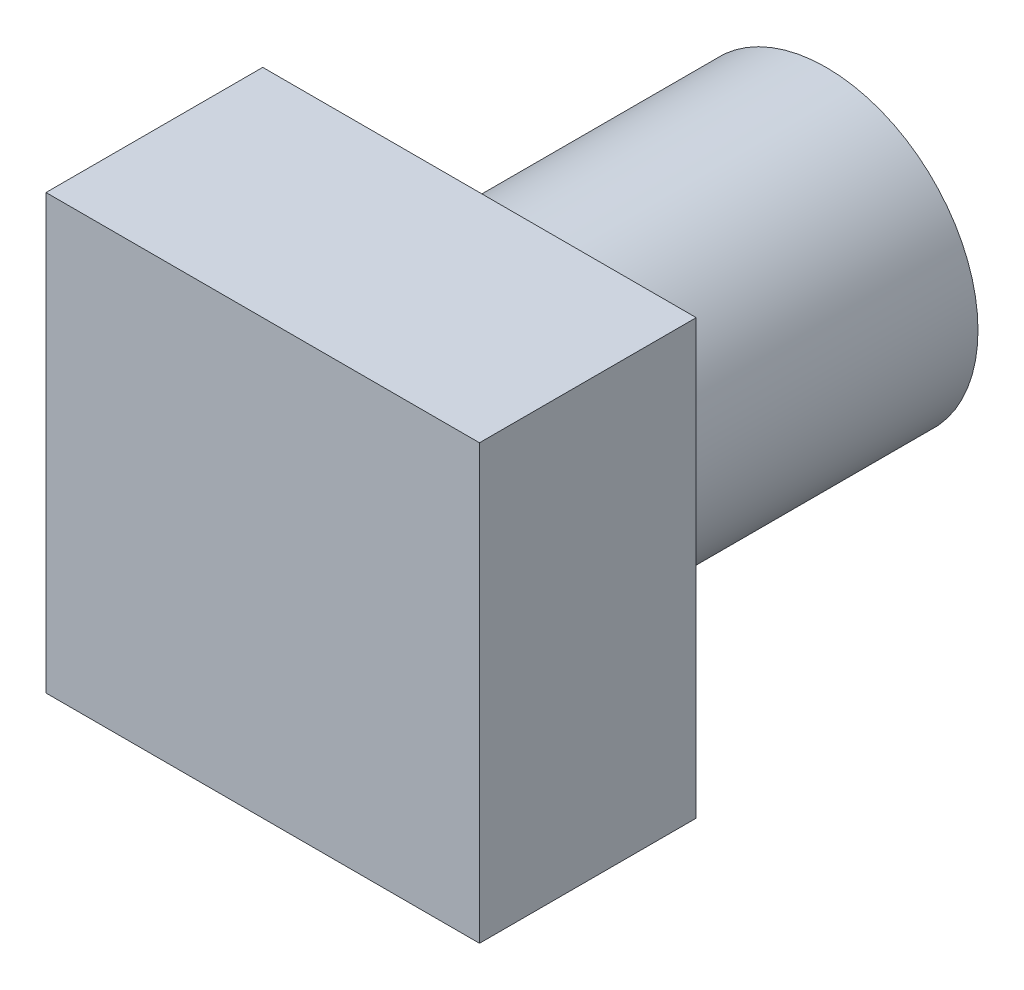
SolidWorks part; units mm, degrees
ref_plane "Front Plane" through (0, 0, 0) normal (0, 0, 1) x (1, 0, 0)
ref_plane "Top Plane" through (0, 0, 0) normal (0, 1, 0) x (1, 0, 0)
ref_plane "Right Plane" through (0, 0, 0) normal (1, 0, 0) x (0, 0, -1)
sketch "Sketch2" plane through (0, 0, 0) normal (0, 0, 1) x (1, 0, 0)
  line L1 (0, 0) -> (10, 0)
  line L2 (0, 0) -> (0, 10)
  line L3 (0, 10) -> (10, 10)
  line L4 (10, 0) -> (10, 10)
  dimension "D1" = 10
  dimension "D2" = 10
extrude "Boss-Extrude1" add sketch "Sketch2" along normal blind 5
sketch "Sketch4" plane through (0, 0, 5) normal (0, 0, 1) x (1, 0, 0)
  line L0 (0, 18.97) -> (0, -8.97)
  line L1 (0, -8.97) -> (15, -8.97)
  line L2 (15, -8.97) -> (15, 18.97)
  line L3 (15, 18.97) -> (0, 18.97)
  line L4 (0, 0) -> (10, 0) construction
  line L7 (10, 0) -> (10, 10) construction
  dimension "D1" = 270
  dimension "D2" = 27.94
  dimension "D3" = 10
  dimension "D4" = 8.97
  dimension "D5" = 15
extrude "Boss-Extrude4" add sketch "Sketch4" along normal blind 4
sketch "Sketch5" plane through (0, 0, 9) normal (0, 0, 1) x (1, 0, 0)
  line L0 (0, -8.97) -> (15, -8.97) construction
  line L1 (15, 18.97) -> (12.7455, 18.97)
  line L2 (15, 18.97) -> (15, -8.97)
  line L3 (15, -8.97) -> (12.7455, -8.97)
  line L4 (12.7455, 18.97) -> (12.7455, -8.97)
extrude "Boss-Extrude5" add sketch "Sketch5" along normal blind 4
sketch "Sketch6" plane through (12.7455, 0, 0) normal (-1, 0, 0) x (0, 0, 1)
  line L0 (9, 18.97) -> (9, -8.97) construction
  line L2 (13, -8.97) -> (9, -8.97) construction
  circle A0 centre (11.286, 16.6443) radius 1.5
  circle A1 centre (11.286, -6.645) radius 1.5
  dimension "D1" = 3
  dimension "D2" = 3
  dimension "D3" = 2.286
  dimension "D4" = 2.286
  dimension "D5" = 23.2893
  dimension "D6" = 2.325
extrude "Cut-Extrude1" cut sketch "Sketch6" against normal blind 40
sketch "Sketch7" plane through (0, 0, 0) normal (0, 0, -1) x (-1, 0, 0)
  line L0 (0, 10) -> (0, 0) construction
  line L1 (-10, 10) -> (0, 10) construction
  circle A0 centre (-5, 5) radius 3.5
  dimension "D1" = 7
  dimension "D2" = 5
  dimension "D3" = 5
extrude "Boss-Extrude6" add sketch "Sketch7" along normal blind 8
sketch "Sketch8" plane through (0, 0, 13) normal (0, 0, 1) x (1, 0, 0)
  line L1 (15, 18.97) -> (0, 18.97)
  line L2 (15, 18.97) -> (15, -8.97)
  line L3 (15, -8.97) -> (0, -8.97)
  line L4 (0, 18.97) -> (0, -8.97)
extrude "Cut-Extrude2" cut sketch "Sketch8" against normal up to surface (8 mm away) up to face at (6.25, 5, 5)
